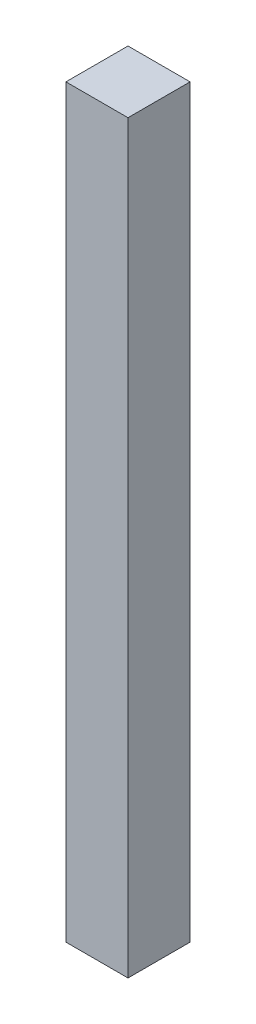
SolidWorks part; units mm, degrees
ref_plane "Front Plane" through (0, 0, 0) normal (0, 0, 1) x (1, 0, 0)
ref_plane "Top Plane" through (0, 0, 0) normal (0, 1, 0) x (1, 0, 0)
ref_plane "Right Plane" through (0, 0, 0) normal (1, 0, 0) x (0, 0, -1)
sketch "Sketch1" plane through (0, 0, 0) normal (0, 0, 1) x (1, 0, 0)
  line L1 (-12.7, -152.4) -> (12.7, -152.4)
  line L2 (-12.7, -152.4) -> (-12.7, 152.4)
  line L3 (-12.7, 152.4) -> (12.7, 152.4)
  line L4 (12.7, -152.4) -> (12.7, 152.4)
  line L5 (-12.7, -152.4) -> (12.7, 152.4) construction
  line L6 (-12.7, 152.4) -> (12.7, -152.4) construction
  point P0 (0, 0)
  dimension "D1" = 25.4
  dimension "D2" = 304.8
extrude "Boss-Extrude1" add sketch "Sketch1" along normal blind 25.4
